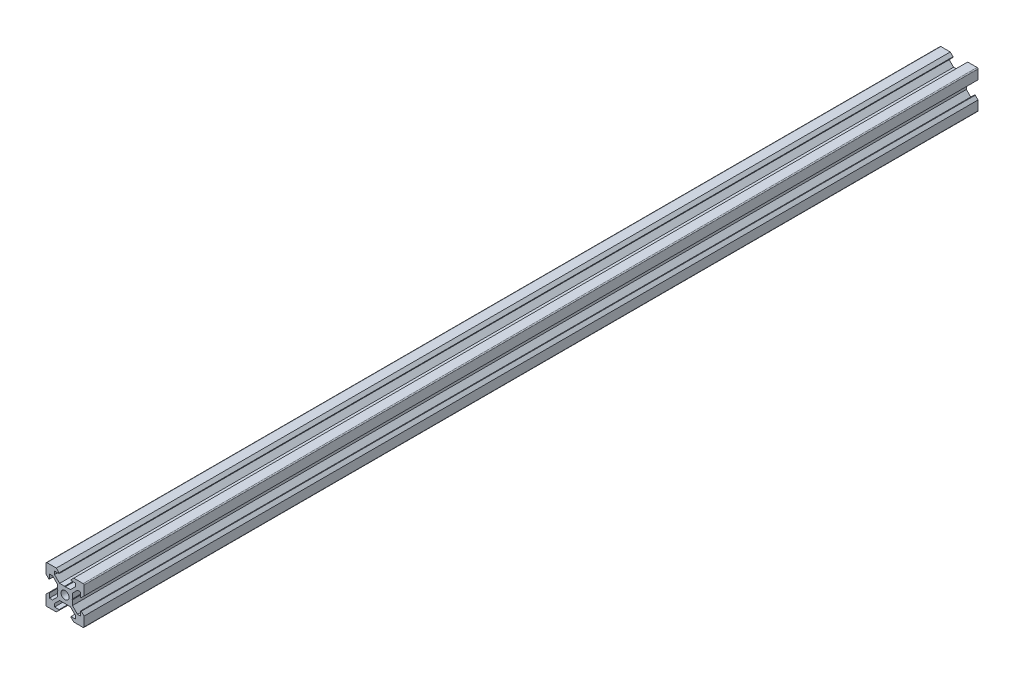
SolidWorks part; units mm, degrees
material "6061-T6 (SS)"
ref_plane "Front Plane" through (0, 0, 0) normal (0, 0, 1) x (1, 0, 0)
ref_plane "Top Plane" through (0, 0, 0) normal (0, 1, 0) x (1, 0, 0)
ref_plane "Right Plane" through (0, 0, 0) normal (1, 0, 0) x (0, 0, -1)
sketch "Sketch1" plane through (0, 0, 0) normal (0, 0, 1) x (1, 0, 0)
  line L1 (9.5, -10) -> (-9.5, -10)
  line L2 (10, -9.5) -> (10, 9.5)
  line L3 (9.5, 10) -> (-9.5, 10)
  line L4 (-10, -9.5) -> (-10, 9.5)
  line L5 (10, -10) -> (-10, 10) construction
  line L6 (10, 10) -> (-10, -10) construction
  circle A0 centre (0, 0) radius 2.1
  arc A1 (-9.5, 10) -> (-10, 9.5) centre (-9.5, 9.5) ccw
  arc A2 (10, 9.5) -> (9.5, 10) centre (9.5, 9.5) ccw
  arc A3 (9.5, -10) -> (10, -9.5) centre (9.5, -9.5) ccw
  arc A4 (-9.5, -10) -> (-10, -9.5) centre (-9.5, -9.5) cw
  point P0 (0, 0)
  line B0 (0, 0) -> (0, 10) construction
  line B1 (0, 3.69) -> (-0.21, 3.9)
  line B2 (-0.21, 3.9) -> (-2.8393, 3.9)
  line B3 (-2.8393, 3.9) -> (-5.5, 6.5607)
  line B4 (-5.5, 6.5607) -> (-5.5, 8.2)
  line B5 (-5.5, 8.2) -> (-3.125, 8.2)
  line B6 (-3.125, 8.2) -> (-3.125, 8.545)
  line B7 (-3.125, 8.545) -> (-4.58, 10)
  line B8 (-4.58, 10) -> (4.58, 10)
  line B9 (0, 0) -> (-5.9132, 5.9132) construction
  line B10 (3.125, 8.545) -> (4.58, 10)
  line B11 (3.125, 8.2) -> (3.125, 8.545)
  line B12 (5.5, 8.2) -> (3.125, 8.2)
  line B13 (5.5, 6.5607) -> (5.5, 8.2)
  line B14 (2.8393, 3.9) -> (5.5, 6.5607)
  line B15 (0.21, 3.9) -> (2.8393, 3.9)
  line B16 (0, 3.69) -> (0.21, 3.9)
  line B17 (0, 0) -> (-10, 0) construction
  line B18 (-3.69, 0) -> (-3.9, -0.21)
  line B19 (-3.9, -0.21) -> (-3.9, -2.8393)
  line B20 (-3.9, -2.8393) -> (-6.5607, -5.5)
  line B21 (-6.5607, -5.5) -> (-8.2, -5.5)
  line B22 (-8.2, -5.5) -> (-8.2, -3.125)
  line B23 (-8.2, -3.125) -> (-8.545, -3.125)
  line B24 (-8.545, -3.125) -> (-10, -4.58)
  line B25 (-10, -4.58) -> (-10, 4.58)
  line B26 (0, 0) -> (-5.9132, -5.9132) construction
  line B27 (-8.545, 3.125) -> (-10, 4.58)
  line B28 (-8.2, 3.125) -> (-8.545, 3.125)
  line B29 (-8.2, 5.5) -> (-8.2, 3.125)
  line B30 (-6.5607, 5.5) -> (-8.2, 5.5)
  line B31 (-3.9, 2.8393) -> (-6.5607, 5.5)
  line B32 (-3.9, 0.21) -> (-3.9, 2.8393)
  line B33 (-3.69, 0) -> (-3.9, 0.21)
  line B34 (0, 0) -> (0, -10) construction
  line B35 (0, -3.69) -> (0.21, -3.9)
  line B36 (0.21, -3.9) -> (2.8393, -3.9)
  line B37 (2.8393, -3.9) -> (5.5, -6.5607)
  line B38 (5.5, -6.5607) -> (5.5, -8.2)
  line B39 (5.5, -8.2) -> (3.125, -8.2)
  line B40 (3.125, -8.2) -> (3.125, -8.545)
  line B41 (3.125, -8.545) -> (4.58, -10)
  line B42 (4.58, -10) -> (-4.58, -10)
  line B43 (0, 0) -> (5.9132, -5.9132) construction
  line B44 (-3.125, -8.545) -> (-4.58, -10)
  line B45 (-3.125, -8.2) -> (-3.125, -8.545)
  line B46 (-5.5, -8.2) -> (-3.125, -8.2)
  line B47 (-5.5, -6.5607) -> (-5.5, -8.2)
  line B48 (-2.8393, -3.9) -> (-5.5, -6.5607)
  line B49 (-0.21, -3.9) -> (-2.8393, -3.9)
  line B50 (0, -3.69) -> (-0.21, -3.9)
  line B51 (0, 0) -> (10, 0) construction
  line B52 (3.69, 0) -> (3.9, 0.21)
  line B53 (3.9, 0.21) -> (3.9, 2.8393)
  line B54 (3.9, 2.8393) -> (6.5607, 5.5)
  line B55 (6.5607, 5.5) -> (8.2, 5.5)
  line B56 (8.2, 5.5) -> (8.2, 3.125)
  line B57 (8.2, 3.125) -> (8.545, 3.125)
  line B58 (8.545, 3.125) -> (10, 4.58)
  line B59 (10, 4.58) -> (10, -4.58)
  line B60 (0, 0) -> (5.9132, 5.9132) construction
  line B61 (8.545, -3.125) -> (10, -4.58)
  line B62 (8.2, -3.125) -> (8.545, -3.125)
  line B63 (8.2, -5.5) -> (8.2, -3.125)
  line B64 (6.5607, -5.5) -> (8.2, -5.5)
  line B65 (3.9, -2.8393) -> (6.5607, -5.5)
  line B66 (3.9, -0.21) -> (3.9, -2.8393)
  line B67 (3.69, 0) -> (3.9, -0.21)
  dimension "D1" = 4.2
  dimension "D3" = 0.5
  dimension "D2" = 20
sketch_block_instance "V Slot 1-4"
sketch_block "V Slot 1" parameters "D1"=10, "D2"=11, "D3"=4.3, "D4"=1.8, "D5"=0.21, "D6"=45, "D7"=9.16, "D8"=1.5, "D9"=6.25
sketch_block_instance "V Slot 1-5"
sketch_block_instance "V Slot 1-6"
sketch_block_instance "V Slot 1-7"
extrude "Boss-Extrude1" add sketch "Sketch1" along normal mid plane 470 contours B67 B52 B53 B54 B55 B56 B57 B58 L2 A2 L3 B10 B11 B12 B13 B14 B15 B16 B1 B2 B3 B4 B5 B6 B7 A1 L4 B27 B28 B29 B30 B31 B32 B33 B18 B19 B20 B21 B22 B23 B24 A4 L1 B44 B45 B46 B47 B48 B49
